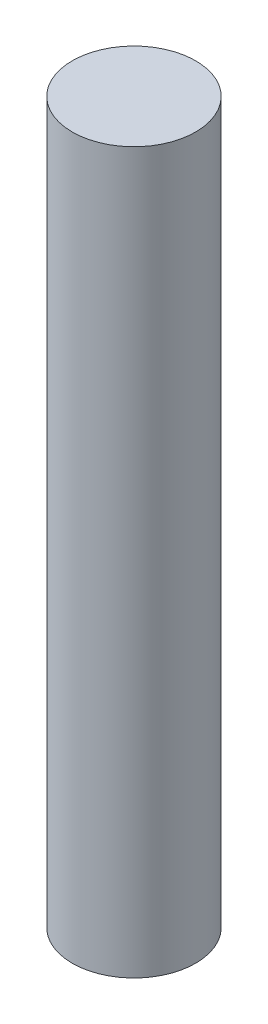
SolidWorks part; units mm, degrees
ref_plane "Front Plane" through (0, 0, 0) normal (0, 0, 1) x (1, 0, 0)
ref_plane "Top Plane" through (0, 0, 0) normal (0, 1, 0) x (1, 0, 0)
ref_plane "Right Plane" through (0, 0, 0) normal (1, 0, 0) x (0, 0, -1)
sketch "Sketch1" plane through (0, 0, 0) normal (0, 1, 0) x (1, 0, 0)
  circle A0 centre (0, 0) radius 3
  dimension "D1" = 6
extrude "Boss-Extrude1" add sketch "Sketch1" along normal blind 35
